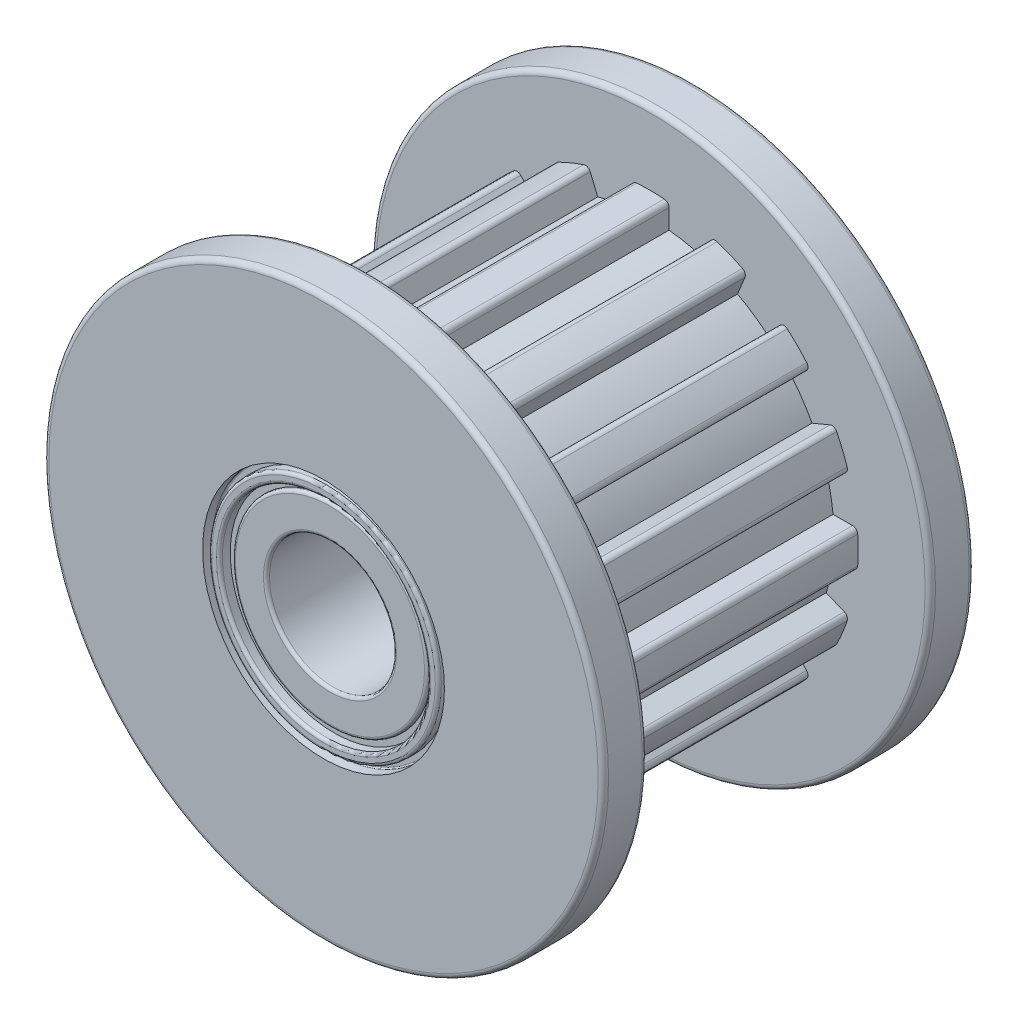
SolidWorks part; units mm, degrees
ref_plane "Plano frontal" through (0, 0, 0) normal (0, 0, 1) x (1, 0, 0)
ref_plane "Plano superior" through (0, 0, 0) normal (0, 1, 0) x (1, 0, 0)
ref_plane "Plano direito" through (0, 0, 0) normal (1, 0, 0) x (0, 0, -1)
sketch "Esboço2" plane through (0, 0, 0) normal (0, 0, 1) x (1, 0, 0)
  line L0 (-0.43, 4.6797) -> (-0.43, 4.2282)
  line L1 (0.43, 4.6797) -> (0.43, 4.2282)
  line L2 (2.1881, 4.159) -> (2.0153, 3.7418)
  line L3 (1.3936, 4.4881) -> (1.2208, 4.0709)
  line L4 (3.6131, 3.005) -> (3.2938, 2.6857)
  line L5 (3.005, 3.6131) -> (2.6857, 3.2938)
  line L6 (4.4881, 1.3936) -> (4.0709, 1.2208)
  line L7 (4.159, 2.1881) -> (3.7418, 2.0153)
  line L8 (4.6797, -0.43) -> (4.2282, -0.43)
  line L9 (4.6797, 0.43) -> (4.2282, 0.43)
  line L10 (4.159, -2.1881) -> (3.7418, -2.0153)
  line L11 (4.4881, -1.3936) -> (4.0709, -1.2208)
  line L12 (3.005, -3.6131) -> (2.6857, -3.2938)
  line L13 (3.6131, -3.005) -> (3.2938, -2.6857)
  line L14 (1.3936, -4.4881) -> (1.2208, -4.0709)
  line L15 (2.1881, -4.159) -> (2.0153, -3.7418)
  line L16 (-0.43, -4.6797) -> (-0.43, -4.2282)
  line L17 (0.43, -4.6797) -> (0.43, -4.2282)
  line L18 (-2.1881, -4.159) -> (-2.0153, -3.7418)
  line L19 (-1.3936, -4.4881) -> (-1.2208, -4.0709)
  line L20 (-3.6131, -3.005) -> (-3.2938, -2.6857)
  line L21 (-3.005, -3.6131) -> (-2.6857, -3.2938)
  line L22 (-4.4881, -1.3936) -> (-4.0709, -1.2208)
  line L23 (-4.159, -2.1881) -> (-3.7418, -2.0153)
  line L24 (-4.6797, 0.43) -> (-4.2282, 0.43)
  line L25 (-4.6797, -0.43) -> (-4.2282, -0.43)
  line L26 (-4.159, 2.1881) -> (-3.7418, 2.0153)
  line L27 (-4.4881, 1.3936) -> (-4.0709, 1.2208)
  line L28 (-3.005, 3.6131) -> (-2.6857, 3.2938)
  line L29 (-3.6131, 3.005) -> (-3.2938, 2.6857)
  line L30 (-1.3936, 4.4881) -> (-1.2208, 4.0709)
  line L31 (-2.1881, 4.159) -> (-2.0153, 3.7418)
  line L32 (-2.0153, -3.7418) -> (-2.0977, -3.6962)
  arc A0 (0.3179, 4.7995) -> (-0.3179, 4.7995) centre (0, 0) ccw
  arc A1 (-3.2938, 2.6857) -> (-3.7418, 2.0153) centre (0, 0) ccw
  arc A2 (0.43, 4.6797) -> (0.3179, 4.7995) centre (0.31, 4.6797) ccw
  arc A3 (-0.3179, 4.7995) -> (-0.43, 4.6797) centre (-0.31, 4.6797) ccw
  arc A4 (2.1881, 4.159) -> (2.1304, 4.3125) centre (2.0773, 4.2049) ccw
  arc A5 (2.1304, 4.3125) -> (1.543, 4.5558) centre (0, 0) ccw
  arc A6 (1.543, 4.5558) -> (1.3936, 4.4881) centre (1.5045, 4.4422) ccw
  arc A7 (-4.0709, 1.2208) -> (-4.2282, 0.43) centre (0, 0) ccw
  arc A8 (3.6131, 3.005) -> (3.6186, 3.1689) centre (3.5283, 3.0899) ccw
  arc A9 (3.6186, 3.1689) -> (3.1689, 3.6186) centre (0, 0) ccw
  arc A10 (3.1689, 3.6186) -> (3.005, 3.6131) centre (3.0899, 3.5283) ccw
  arc A11 (-4.2282, -0.43) -> (-4.0709, -1.2208) centre (0, 0) ccw
  arc A12 (4.4881, 1.3936) -> (4.5558, 1.543) centre (4.4422, 1.5045) ccw
  arc A13 (4.5558, 1.543) -> (4.3125, 2.1304) centre (0, 0) ccw
  arc A14 (4.3125, 2.1304) -> (4.159, 2.1881) centre (4.2049, 2.0773) ccw
  arc A15 (-3.7418, -2.0153) -> (-3.2938, -2.6857) centre (0, 0) ccw
  arc A16 (4.6797, -0.43) -> (4.7995, -0.3179) centre (4.6797, -0.31) ccw
  arc A17 (4.7995, -0.3179) -> (4.7995, 0.3179) centre (0, 0) ccw
  arc A18 (4.7995, 0.3179) -> (4.6797, 0.43) centre (4.6797, 0.31) ccw
  arc A19 (-2.6857, -3.2938) -> (-2.0977, -3.6962) centre (0, 0) ccw
  arc A20 (4.159, -2.1881) -> (4.3125, -2.1304) centre (4.2049, -2.0773) ccw
  arc A21 (4.3125, -2.1304) -> (4.5558, -1.543) centre (0, 0) ccw
  arc A22 (4.5558, -1.543) -> (4.4881, -1.3936) centre (4.4422, -1.5045) ccw
  arc A23 (-1.2208, -4.0709) -> (-0.43, -4.2282) centre (0, 0) ccw
  arc A24 (3.005, -3.6131) -> (3.1689, -3.6186) centre (3.0899, -3.5283) ccw
  arc A25 (3.1689, -3.6186) -> (3.6186, -3.1689) centre (0, 0) ccw
  arc A26 (3.6186, -3.1689) -> (3.6131, -3.005) centre (3.5283, -3.0899) ccw
  arc A27 (0.43, -4.2282) -> (1.2208, -4.0709) centre (0, 0) ccw
  arc A28 (1.3936, -4.4881) -> (1.543, -4.5558) centre (1.5045, -4.4422) ccw
  arc A29 (1.543, -4.5558) -> (2.1304, -4.3125) centre (0, 0) ccw
  arc A30 (2.1304, -4.3125) -> (2.1881, -4.159) centre (2.0773, -4.2049) ccw
  arc A31 (2.0153, -3.7418) -> (2.6857, -3.2938) centre (0, 0) ccw
  arc A32 (-0.43, -4.6797) -> (-0.3179, -4.7995) centre (-0.31, -4.6797) ccw
  arc A33 (-0.3179, -4.7995) -> (0.3179, -4.7995) centre (0, 0) ccw
  arc A34 (0.3179, -4.7995) -> (0.43, -4.6797) centre (0.31, -4.6797) ccw
  arc A35 (3.2938, -2.6857) -> (3.7418, -2.0153) centre (0, 0) ccw
  arc A36 (-2.1881, -4.159) -> (-2.1304, -4.3125) centre (-2.0773, -4.2049) ccw
  arc A37 (-2.1304, -4.3125) -> (-1.543, -4.5558) centre (0, 0) ccw
  arc A38 (-1.543, -4.5558) -> (-1.3936, -4.4881) centre (-1.5045, -4.4422) ccw
  arc A39 (4.0709, -1.2208) -> (4.2282, -0.43) centre (0, 0) ccw
  arc A40 (-3.6131, -3.005) -> (-3.6186, -3.1689) centre (-3.5283, -3.0899) ccw
  arc A41 (-3.6186, -3.1689) -> (-3.1689, -3.6186) centre (0, 0) ccw
  arc A42 (-3.1689, -3.6186) -> (-3.005, -3.6131) centre (-3.0899, -3.5283) ccw
  arc A43 (4.2282, 0.43) -> (4.0709, 1.2208) centre (0, 0) ccw
  arc A44 (-4.4881, -1.3936) -> (-4.5558, -1.543) centre (-4.4422, -1.5045) ccw
  arc A45 (-4.5558, -1.543) -> (-4.3125, -2.1304) centre (0, 0) ccw
  arc A46 (-4.3125, -2.1304) -> (-4.159, -2.1881) centre (-4.2049, -2.0773) ccw
  arc A47 (3.7418, 2.0153) -> (3.2938, 2.6857) centre (0, 0) ccw
  arc A48 (-4.6797, 0.43) -> (-4.7995, 0.3179) centre (-4.6797, 0.31) ccw
  arc A49 (-4.7995, 0.3179) -> (-4.7995, -0.3179) centre (0, 0) ccw
  arc A50 (-4.7995, -0.3179) -> (-4.6797, -0.43) centre (-4.6797, -0.31) ccw
  arc A51 (2.6857, 3.2938) -> (2.0153, 3.7418) centre (0, 0) ccw
  arc A52 (-4.159, 2.1881) -> (-4.3125, 2.1304) centre (-4.2049, 2.0773) ccw
  arc A53 (-4.3125, 2.1304) -> (-4.5558, 1.543) centre (0, 0) ccw
  arc A54 (-4.5558, 1.543) -> (-4.4881, 1.3936) centre (-4.4422, 1.5045) ccw
  arc A55 (1.2208, 4.0709) -> (0.43, 4.2282) centre (0, 0) ccw
  arc A56 (-3.005, 3.6131) -> (-3.1689, 3.6186) centre (-3.0899, 3.5283) ccw
  arc A57 (-3.1689, 3.6186) -> (-3.6186, 3.1689) centre (0, 0) ccw
  arc A58 (-3.6186, 3.1689) -> (-3.6131, 3.005) centre (-3.5283, 3.0899) ccw
  arc A59 (-0.43, 4.2282) -> (-1.2208, 4.0709) centre (0, 0) ccw
  arc A60 (-1.3936, 4.4881) -> (-1.543, 4.5558) centre (-1.5045, 4.4422) ccw
  arc A61 (-1.543, 4.5558) -> (-2.1304, 4.3125) centre (0, 0) ccw
  arc A62 (-2.1304, 4.3125) -> (-2.1881, 4.159) centre (-2.0773, 4.2049) ccw
  arc A63 (-2.0153, 3.7418) -> (-2.6857, 3.2938) centre (0, 0) ccw
  point P148 (0, 0)
  dimension "D1" = 9.62
  dimension "D3" = 0.12
  dimension "D4" = 16
extrude "Ressalto-extrusão3" add sketch "Esboço2" along normal blind 6.55
sketch "Esboço3" plane through (0, 0, 6.55) normal (0, 0, 1) x (1, 0, 0)
  circle A0 centre (0, 0) radius 6.48
  dimension "D1" = 12.96
extrude "Ressalto-extrusão4" add sketch "Esboço3" along normal blind 1.02
sketch "Esboço4" plane through (0, 0, 0) normal (0, 0, -1) x (-1, 0, 0)
  circle A0 centre (0, 0) radius 6.48
extrude "Ressalto-extrusão5" add sketch "Esboço4" along normal blind 1.02
fillet "Filete2" radius 0.12 4 edges at (6.48, 0, 6.55) (-6.48, 0, -1.02) (-6.48, 0, 0) (6.48, 0, 7.57)
sketch "Esboço5" plane through (0, 0, 7.57) normal (0, 0, 1) x (1, 0, 0)
  circle A0 centre (0, 0) radius 1.47
  dimension "D1" = 2.94
extrude "Corte-extrusão1" cut sketch "Esboço5" against normal blind 10.02 and the other way blind 10
sketch "Esboço6" plane through (0, 0, 7.57) normal (0, 0, 1) x (1, 0, 0)
  circle A0 centre (0, 0) radius 2.26
  circle A1 centre (0, 0) radius 1.47 construction
  dimension "D1" = 0.79
extrude "Corte-extrusão3" cut sketch "Esboço6" against normal blind 0.15
sketch "Esboço8" plane through (0, 0, -1.02) normal (0, 0, -1) x (-1, 0, 0)
  circle A0 centre (0, 0) radius 2.26
  dimension "D1" = 4.52
extrude "Corte-extrusão4" cut sketch "Esboço8" against normal blind 0.15
sketch "Esboço9" plane through (0, 0, 7.57) normal (0, 0, 1) x (1, 0, 0)
  circle A0 centre (0, 0) radius 2.26
  circle A1 centre (0, 0) radius 2.41
  dimension "D1" = 0.15
extrude "Corte-extrusão7" cut sketch "Esboço9" against normal blind 0.25
sketch "Esboço11" plane through (0, 0, -1.02) normal (0, 0, -1) x (-1, 0, 0)
  circle A0 centre (0, 0) radius 2.26
  circle A1 centre (0, 0) radius 2.46
  dimension "D1" = 0.2
extrude "Corte-extrusão8" cut sketch "Esboço11" against normal blind 0.25
fillet "Filete4" radius 0.07 2 edges at (-2.26, 0, -0.87) (-1.47, 0, -0.87)
fillet "Filete5" radius 0.07 2 edges at (2.26, 0, 7.42) (1.47, 0, 7.42)
sketch "Esboço12" plane through (0, 0, 7.57) normal (0, 0, 1) x (1, 0, 0)
  circle A1 centre (0, 0) radius 2.66
  circle A2 centre (0, 0) radius 2.8
  dimension "D2" = 5.6
extrude "Corte-extrusão10" cut sketch "Esboço12" against normal blind 0.25
fillet "Filete6" radius 0.07 2 edges at (2.66, 0, 7.57) (2.41, 0, 7.57)
fillet "Filete7" radius 0.03 1 edges at (2.8, 0, 7.32)
sketch "Esboço13" plane through (0, 0, -1.02) normal (0, 0, -1) x (-1, 0, 0)
  circle A0 centre (0, 0) radius 2.65
  circle A1 centre (0, 0) radius 2.8
  dimension "D1" = 5.6
  dimension "D2" = 0.15
extrude "Corte-extrusão11" cut sketch "Esboço13" against normal blind 0.25
fillet "Filete8" radius 0.03 2 edges at (-2.65, 0, -1.02) (-2.46, 0, -1.02)
fillet "Filete9" radius 0.07 1 edges at (-2.8, 0, -1.02)
